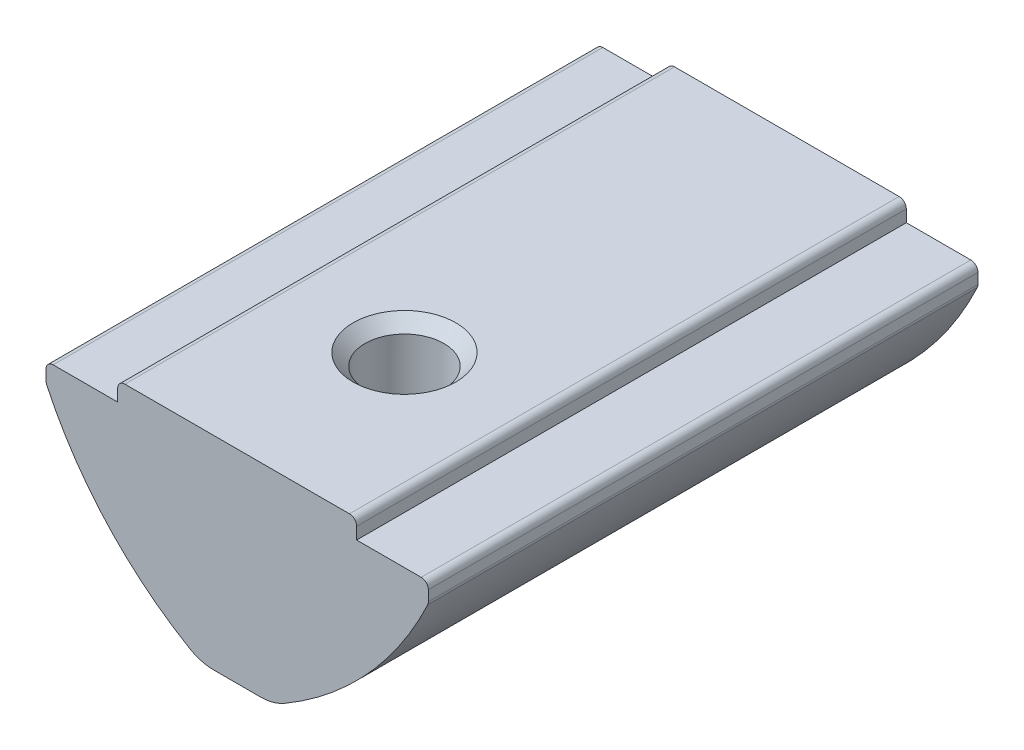
SolidWorks part; units mm, degrees
ref_plane "Спереди" through (0, 0, 0) normal (0, 0, 1) x (1, 0, 0)
ref_plane "Сверху" through (0, 0, 0) normal (0, 1, 0) x (1, 0, 0)
ref_plane "Справа" through (0, 0, 0) normal (1, 0, 0) x (0, 0, -1)
sketch "Эскиз1" plane through (0, 0, 0) normal (0, 0, 1) x (1, 0, 0)
  line L0 (-5, 0) -> (5, 0)
  line L5 (-5, 0) -> (-5, -0.8)
  line L6 (-5, -0.8) -> (-8, -0.8)
  line L7 (-8, -0.8) -> (-8, -1.6)
  line L8 (5, 0) -> (5, -0.8)
  line L9 (5, -0.8) -> (8, -0.8)
  line L10 (8, -0.8) -> (8, -1.6)
  line L11 (-1.5, -8.5) -> (1.5, -8.5)
  arc A0 (-8, -1.6) -> (-1.5, -8.5) centre (5.609, 4.7084) ccw
  arc A1 (1.5, -8.5) -> (8, -1.6) centre (-5.609, 4.7084) ccw
  point P0 (0, -8.5)
  point P4 (0, 0)
  dimension "D7" = 15
  dimension "D1" = 10
  dimension "D2" = 16
  dimension "D3" = 0.8
  dimension "D4" = 3
  dimension "D5" = 0.8
  dimension "D6" = 8.5
extrude "Бобышка-Вытянуть1" add sketch "Эскиз1" along normal mid plane 23
fillet "Скругление1" radius 0.3 6 edges at (8, -1.6, 0) (8, -0.8, 0) (-8, -0.8, 0) (-8, -1.6, 0) (5, 0, 0) (-5, 0, 0)
fillet "Скругление2" radius 2 2 edges at (1.5, -8.5, 0) (-1.5, -8.5, 0)
hole_wizard "Отверстие обработанное метчиком M42" positions "Эскиз2" profile "Эскиз4" tap size "M4" standard "ISO" end condition through all
sketch "Эскиз2" plane through (0, 0, 0) normal (0, 1, 0) x (1, 0, 0)
  line L0 (4.7, -11.5) -> (-4.7, -11.5) construction
  point P0 (0, -4.5)
  dimension "D1" = 7
sketch "Эскиз4" plane through (0, 0, 4.5) normal (1, 0, 0) x (0, 0, 1)
  line L0 (0, 0) -> (0, 8.5)
  line L1 (0, 8.5) -> (1.65, 8.5)
  line L2 (1.65, 8.5) -> (1.65, 0.5)
  line L3 (1.65, 0.5) -> (2.15, 0)
  line L5 (2.15, 0) -> (0, 0)
  line L6 (-1.65, 0.5) -> (-2.15, 0) construction
  line L11 (0, -6.35) -> (0, 107.95) construction
  dimension "Диаметр проходного сверла" = 3.3
  dimension "Глубина проходного сверла" = 8.5
  dimension "Диаметр передней зенковки" = 4.3
  dimension "Угол передней зенковки" = 90
cosmetic thread "Отверстие резьбы1" parameters "D2"=4
sketch "Эскиз5" plane through (0, 0, 0) normal (1, 0, 0) x (0, 0, -1)
  line L1 (6.5, -4.3) -> (6.5, -9.3) construction
  line L2 (11.5, -8.2244) -> (11.5, -1.6609) construction
  line L3 (6.5, -4.3) -> (6.5, -9.3)
  line L5 (11.5, -8.5) -> (-3.1701, -8.5) construction
  arc A0 (6.5, -4.3) -> (6.5, -9.3) centre (6.5, -6.8) ccw
  point P3 (4, -7.4722)
  dimension "D3" = 2.5
  dimension "D1" = 0.8
  dimension "D2" = 5
revolve "Повернуть1" add sketch "Эскиз5" angle 360 about L1
